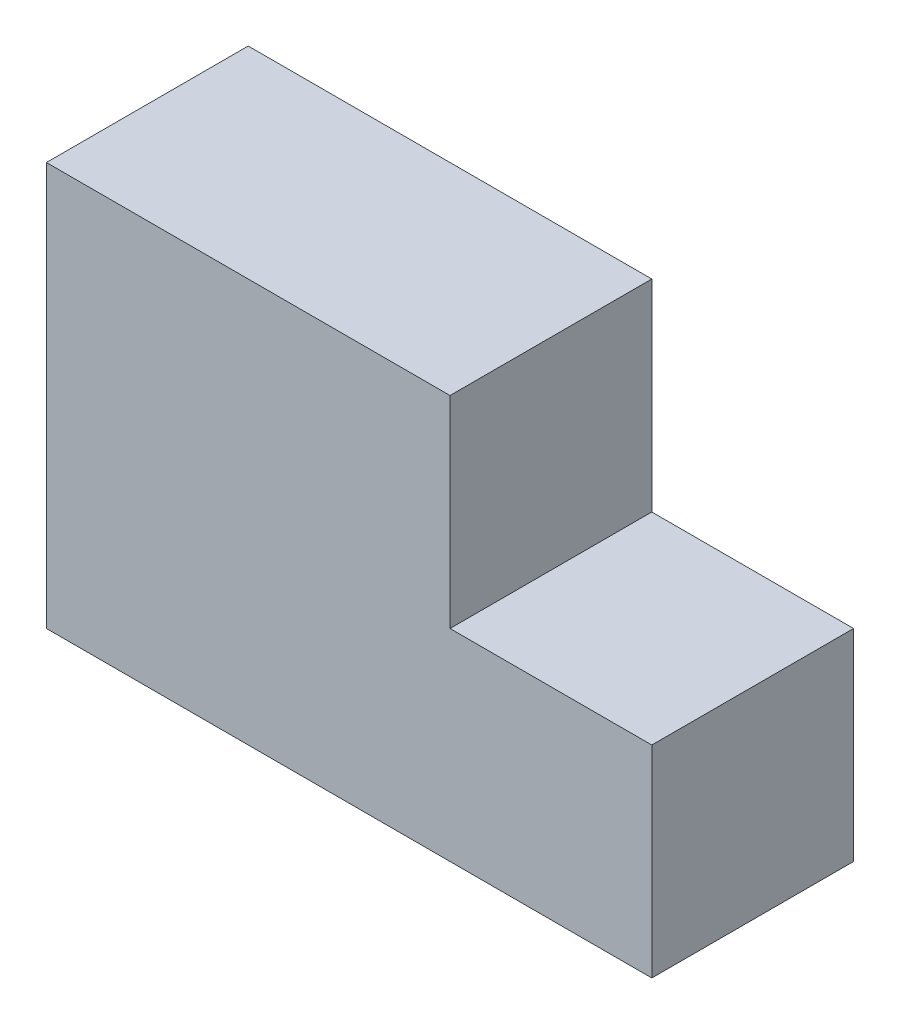
SolidWorks part; units mm, degrees
ref_plane "Front Plane" through (0, 0, 0) normal (0, 0, 1) x (1, 0, 0)
ref_plane "Top Plane" through (0, 0, 0) normal (0, 1, 0) x (1, 0, 0)
ref_plane "Right Plane" through (0, 0, 0) normal (1, 0, 0) x (0, 0, -1)
sketch "Sketch1" plane through (0, 0, 0) normal (0, 0, 1) x (1, 0, 0)
  line L14 (0, 50.8) -> (50.8, 50.8)
  line L15 (50.8, 50.8) -> (50.8, 25.4)
  line L16 (50.8, 25.4) -> (76.2, 25.4)
  line L17 (76.2, 25.4) -> (76.2, 0)
  line L18 (76.2, 0) -> (0, 0)
  line L19 (0, 0) -> (0, 50.8)
extrude "Boss-Extrude1" add sketch "Sketch1" along normal blind 25.4
